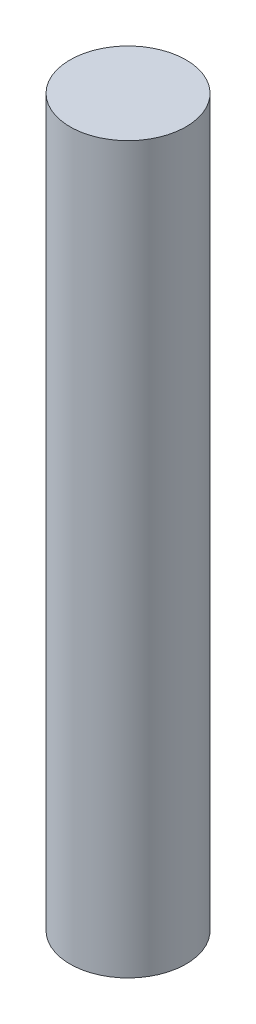
SolidWorks part; units mm, degrees
ref_plane "Plan de face" through (0, 0, 0) normal (0, 0, 1) x (1, 0, 0)
ref_plane "Plan de dessus" through (0, 0, 0) normal (0, 1, 0) x (1, 0, 0)
ref_plane "Plan de droite" through (0, 0, 0) normal (1, 0, 0) x (0, 0, -1)
sketch "Esquisse1" plane through (0, 0, 0) normal (0, 0, 1) x (1, 0, 0)
  line L0 (2.5, 0) -> (4, 0)
  line L1 (4, 0) -> (4, 50)
  line L2 (4, 50) -> (0, 50)
  line L3 (2.5, 0) -> (2.5, 10)
  line L4 (2.5, 10) -> (0, 10)
  line L5 (0, 10) -> (0, 50) construction
  line L6 (0, 50) -> (0, 10)
  line L7 (0, 0) -> (0, 10) construction
  dimension "D1" = 4
  dimension "D2" = 40
  dimension "D3" = 50
  dimension "D4" = 1.5
revolve "Révolution1" add sketch "Esquisse1" angle 360 about L5
